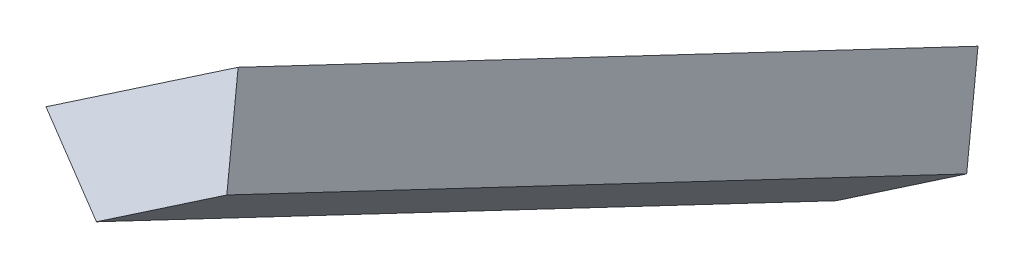
SolidWorks part; units mm, degrees
ref_plane "Front Plane" through (0, 0, 0) normal (0, 0, 1) x (1, 0, 0)
ref_plane "Top Plane" through (0, 0, 0) normal (0, 1, 0) x (1, 0, 0)
ref_plane "Right Plane" through (0, 0, 0) normal (1, 0, 0) x (0, 0, -1)
sketch "Sketch2" plane through (8.2776, 23.1075, 39.4767) normal (0.1781, 0.4971, 0.8492) x (0.984, -0.09, -0.1537)
  line L0 (-19.3214, 76.5713) -> (-19.7987, 76.2419)
  line L1 (-19.7987, 76.2419) -> (-20.1793, 76.5555)
  line L2 (-20.1793, 76.5555) -> (-19.4758, 77.041)
  line L3 (-19.4758, 77.041) -> (-19.3214, 76.5713)
  line L4 (-13.4835, 81.1767) -> (-51.514, 54.9294) construction
  dimension "D1" = 0.58
extrude "Boss-Extrude2" add sketch "Sketch2" along normal blind 6
